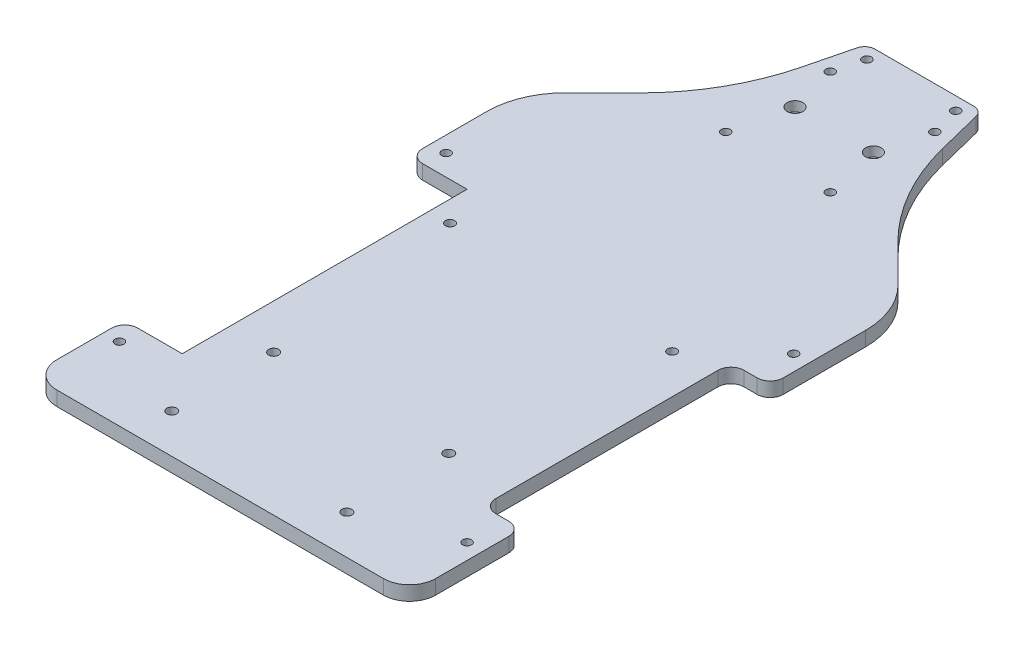
SolidWorks part; units mm, degrees
ref_plane "정면" through (0, 0, 0) normal (0, 0, 1) x (1, 0, 0)
ref_plane "윗면" through (0, 0, 0) normal (0, 1, 0) x (1, 0, 0)
ref_plane "우측면" through (0, 0, 0) normal (1, 0, 0) x (0, 0, -1)
sketch "스케치1" plane through (0, 0, 0) normal (0, 1, 0) x (1, 0, 0)
  line L0 (-857.021, 0) -> (41994.0268, 0) construction
  line L1 (0, -857.021) -> (0, 41994.0268) construction
  line L2 (-72.5, 0) -> (-72.5, -180)
  line L3 (-72.5, 95) -> (72.5, 95) construction
  line L4 (-72.5, 95) -> (-72.5, -190) construction
  line L5 (-72.5, -190) -> (-47.5, -190) construction
  line L6 (72.5, 95) -> (72.5, -190) construction
  line L7 (-62.5, -190) -> (-49.1961, -190)
  line L8 (72.5, -180) -> (72.5, 0)
  line L9 (-15.8039, -213) -> (15.8039, -213)
  line L14 (-18.846, -211.968) -> (-46.154, -191.032)
  line L15 (-22, 95) -> (22, 95)
  line L16 (-63.6708, 21.2555) -> (-49.4782, 35.3915)
  line L17 (18.846, -211.968) -> (46.154, -191.032)
  line L18 (857.021, 0) -> (-41994.0268, 0) construction
  line L23 (47.5, -190) -> (72.5, -190) construction
  line L24 (49.1961, -190) -> (62.5, -190)
  line L25 (-27, 75) -> (-22, 95)
  line L26 (63.6708, 21.2555) -> (49.4782, 35.3915)
  line L27 (27, 75) -> (22, 95)
  arc A4 (62.5, -190) -> (72.5, -180) centre (62.5, -180) ccw
  arc A5 (-62.5, -190) -> (-72.5, -180) centre (-62.5, -180) cw
  arc A12 (49.1961, -190) -> (46.154, -191.032) centre (49.1961, -195) ccw
  arc A13 (18.846, -211.968) -> (15.8039, -213) centre (15.8039, -208) cw
  arc A14 (-15.8039, -213) -> (-18.846, -211.968) centre (-15.8039, -208) cw
  arc A15 (-49.1961, -190) -> (-46.154, -191.032) centre (-49.1961, -195) cw
  arc A16 (-72.5, 0) -> (-63.6708, 21.2555) centre (-42.5, 0) cw
  arc A17 (-49.4782, 35.3915) -> (-27, 75) centre (-109.4621, 95.6155) ccw
  arc A18 (72.5, 0) -> (63.6708, 21.2555) centre (42.5, 0) ccw
  arc A19 (49.4782, 35.3915) -> (27, 75) centre (109.4621, 95.6155) cw
  point P4 (0, 0)
  point P36 (0, -213)
  point P40 (0, 95)
  point P77 (17.5, -213)
  point P80 (-17.5, -213)
  dimension "D8" = 10
  dimension "D13" = 72.5
  dimension "D14" = 5
  dimension "D17" = 20
  dimension "D15" = 30
  dimension "D16" = 85
  dimension "D1" = 145
  dimension "D2" = 285
  dimension "D3" = 190
  dimension "D9" = 35
  dimension "D10" = 23
  dimension "D11" = 25
  dimension "D12" = 44
  dimension "D18" = 5
extrude "Deck base" add sketch "스케치1" along normal blind 5.5 contours L2 A5 L7 A15 L14 A14 L9 A13 L17 A12 L24 A4 L8 A18 L26 A19 L27 L15 L25 A17 L16 A16
sketch "스케치3" plane through (0, 5.5, 0) normal (0, 1, 0) x (1, 0, 0)
  line L0 (-22, 95) -> (22, 95) construction
  line L2 (72.5, -180) -> (72.5, 0) construction
  line L3 (66.5, -146.5) -> (66.5, 0) construction
  line L4 (-200857.021, 0) -> (241994.0268, 0) construction
  line L5 (0, -3.025) -> (0, 3.025) construction
  line L6 (0, -200857.021) -> (0, 241994.0268) construction
  circle A0 centre (17, 90) radius 1.7
  circle A1 centre (66.5, -146.5) radius 1.7
  circle A2 centre (66.5, -116.5) radius 1.7
  circle A3 centre (66.5, -51.5) radius 1.7
  circle A4 centre (66.5, -21.5) radius 1.7
  circle A5 centre (-66.5, -21.5) radius 1.7
  circle A6 centre (-66.5, -51.5) radius 1.7
  circle A7 centre (-66.5, -116.5) radius 1.7
  circle A8 centre (-66.5, -146.5) radius 1.7
  circle A9 centre (-17, 90) radius 1.7
  dimension "D1" = 3.4
  dimension "D3" = 3.4
  dimension "D6" = 3.4
  dimension "D8" = 3.4
  dimension "D9" = 3.4
  dimension "D2" = 5
  dimension "D4" = 111.5
  dimension "D5" = 6
  dimension "D7" = 30
  dimension "D10" = 65
  dimension "D11" = 30
  dimension "D12" = 17
extrude "Bolt slot" cut sketch "스케치3" against normal up to next
fillet "필렛1" radius 4 2 edges at (22, 2.75, -95) (-22, 2.75, -95)
sketch "스케치11" plane through (0, 5.5, 0) normal (0, 1, 0) x (1, 0, 0)
  line L0 (-72.5, 0) -> (-72.5, -180) construction
  line L1 (-72.5, -29.5) -> (-50.5, -29.5)
  line L2 (-72.5, -29.5) -> (-72.5, -138.5)
  line L3 (-72.5, -138.5) -> (-50.5, -138.5)
  line L4 (-50.5, -29.5) -> (-50.5, -138.5)
  line L5 (0, 95) -> (0, -174.2944) construction
  line L6 (-22, 95) -> (22, 95) construction
  line L7 (0, -200857.021) -> (0, 241994.0268) construction
  line L8 (72.5, -131.5) -> (57.5, -131.5)
  line L9 (57.5, -36.5) -> (57.5, -131.5)
  line L10 (72.5, -36.5) -> (57.5, -36.5)
  line L11 (72.5, -36.5) -> (72.5, -131.5)
  line L12 (72.5, -180) -> (72.5, 0) construction
  circle A0 centre (-66.5, -21.5) radius 1.7 construction
  circle A1 centre (-66.5, -146.5) radius 1.7 construction
  circle A2 centre (66.5, -21.5) radius 1.7 construction
  circle A3 centre (66.5, -146.5) radius 1.7 construction
  point P22 (-50.5, -84)
  point P23 (57.5, -84)
  dimension "D2" = 8
  dimension "D3" = 8
  dimension "D5" = 15
  dimension "D1" = 22
  dimension "D4" = 15
  dimension "D6" = 15
  dimension "D7" = 15
extrude "컷-돌출2" cut sketch "스케치11" against normal up to next
sketch "스케치10" plane through (0, 5.5, 0) normal (0, 1, 0) x (1, 0, 0)
  line L0 (-72.5, 0) -> (-72.5, -180) construction
  line L1 (-72.5, -174.5) -> (72.5, -174.5)
  line L2 (-72.5, -174.5) -> (-72.5, -213)
  line L3 (-72.5, -213) -> (72.5, -213)
  line L4 (72.5, -174.5) -> (72.5, -213)
  line L5 (72.5, -180) -> (72.5, 0) construction
  line L6 (-15.8039, -213) -> (15.8039, -213) construction
  circle A0 centre (-66.5, -146.5) radius 1.7 construction
  dimension "D1" = 28
extrude "컷-돌출1" cut sketch "스케치10" against normal up to next
fillet "필렛2" radius 10 2 edges at (72.5, 2.75, 174.5) (-72.5, 2.75, 174.5)
fillet "필렛3" radius 5 6 edges at (57.5, 2.75, 36.5) (72.5, 2.75, 36.5) (57.5, 2.75, 131.5) (72.5, 2.75, 131.5) (-72.5, 2.75, 138.5) (-72.5, 2.75, 29.5)
sketch "스케치4" plane through (0, 5.5, 0) normal (0, 1, 0) x (1, 0, 0)
  line L0 (-22, 95) -> (22, 95) construction
  line L1 (-20, 79) -> (20, 79) construction
  line L2 (-20, 79) -> (-20, 39) construction
  line L3 (-20, 39) -> (20, 39) construction
  line L4 (20, 79) -> (20, 39) construction
  line L5 (0, -200857.021) -> (0, 241994.0268) construction
  line L6 (0, -3.025) -> (0, 3.025) construction
  circle A0 centre (-20, 79) radius 1.7
  circle A1 centre (-20, 39) radius 1.7
  circle A2 centre (20, 39) radius 1.7
  circle A3 centre (20, 79) radius 1.7
  point P6 (0, 79)
  dimension "D4" = 3.4
  dimension "D5" = 3.4
  dimension "D1" = 40
  dimension "D2" = 40
  dimension "D3" = 16
extrude "Lidar slot" cut sketch "스케치4" against normal up to next
sketch "스케치9" plane through (0, 5.5, 0) normal (0, 1, 0) x (1, 0, 0)
  line L0 (0, -200857.021) -> (0, 241994.0268) construction
  line L1 (-24.5, 84) -> (24.5, 84) construction
  line L2 (-24.5, 84) -> (-24.5, 34) construction
  line L3 (-24.5, 34) -> (-12.5, 34) construction
  line L4 (24.5, 84) -> (24.5, 34) construction
  line L5 (-24.5, 84) -> (24.5, 34) construction
  line L6 (-24.5, 34) -> (24.5, 84) construction
  line L7 (-12.5, 29) -> (12.5, 29) construction
  line L8 (-20, 79) -> (20, 79) construction
  line L9 (12.5, 29) -> (12.5, 34) construction
  line L10 (-12.5, 29) -> (-12.5, 34) construction
  line L11 (12.5, 34) -> (24.5, 34) construction
  point P0 (0, 59)
  point P11 (0, 29)
  dimension "D1" = 49
  dimension "D2" = 50
  dimension "D3" = 5
  dimension "D4" = 25
  dimension "D5" = 5
sketch "스케치6" plane through (0, 5.5, 0) normal (0, 1, 0) x (1, 0, 0)
  line L0 (0, -200857.021) -> (0, 241994.0268) construction
  line L1 (-37, -103.5) -> (37, -103.5) construction
  line L2 (-37, -103.5) -> (-37, -174.5) construction
  line L3 (-37, -174.5) -> (37, -174.5) construction
  line L4 (37, -103.5) -> (37, -174.5) construction
  line L6 (0, -3.025) -> (0, 3.025) construction
  line L7 (-12.5, 29) -> (12.5, 29) construction
  circle A0 centre (33.5, -120.5) radius 1.9
  circle A1 centre (33.5, -159.5) radius 1.9
  circle A2 centre (-33.5, -159.5) radius 1.9
  circle A3 centre (-33.5, -120.5) radius 1.9
  point P4 (0, -103.5)
  dimension "D3" = 3.8
  dimension "D6" = 3.8
  dimension "D1" = 74
  dimension "D2" = 71
  dimension "D4" = 17
  dimension "D5" = 3.5
  dimension "D7" = 3.5
  dimension "D8" = 15
  dimension "D9" = 132.5
extrude "Vesc slot" cut sketch "스케치6" against normal up to next
sketch "스케치7" plane through (0, 5.5, 0) normal (0, 1, 0) x (1, 0, 0)
  line L0 (0, -200857.021) -> (0, 241994.0268) construction
  line L1 (-56, 14) -> (56, 14) construction
  line L2 (-56, 14) -> (-56, -102) construction
  line L3 (-56, -102) -> (56, -102) construction
  line L4 (56, 14) -> (56, -102) construction
  line L7 (12.5, 34) -> (24.5, 34) construction
  circle A4 centre (-42.5, -44) radius 1.75
  circle A5 centre (42.5, -44) radius 1.75
  point P4 (0, 14)
  dimension "D6" = 58
  dimension "D7" = 3.5
  dimension "D8" = 3.5
  dimension "D1" = 116
  dimension "D2" = 112
  dimension "D3" = 20
  dimension "D4" = 13.5
  dimension "D5" = 13.5
extrude "Nano slot" cut sketch "스케치7" against normal up to next
sketch "스케치12" plane through (0, 5.5, 0) normal (0, 1, 0) x (1, 0, 0)
  line L0 (-24.5, 34) -> (24.5, 84) construction
  line L1 (-12, 75.5) -> (12, 75.5) construction
  line L2 (-12, 75.5) -> (-12, 42.5) construction
  line L3 (-12, 42.5) -> (12, 42.5) construction
  line L4 (12, 75.5) -> (12, 42.5) construction
  line L5 (-12, 75.5) -> (12, 42.5) construction
  line L6 (-12, 42.5) -> (12, 75.5) construction
  circle A0 centre (-15, 60.5) radius 1.75
  circle A1 centre (15, 60.5) radius 1.75
  point P0 (0, 59)
  dimension "D3" = 3.5
  dimension "D4" = 3.5
  dimension "D1" = 24
  dimension "D2" = 33
  dimension "D5" = 15
  dimension "D6" = 15
  dimension "D7" = 15
extrude "컷-돌출3" cut sketch "스케치12" against normal up to next
sketch "스케치13" plane through (0, 5.5, 0) normal (0, 1, 0) x (1, 0, 0)
  circle A0 centre (-15, 60.5) radius 3
  circle A1 centre (15, 60.5) radius 3
  dimension "D1" = 6
  dimension "D2" = 6
extrude "컷-돌출4" cut sketch "스케치13" against normal blind 3.7
chamfer "모따기1" distance 4 angle 45 1 edges at (-50.5, 0, 84)
